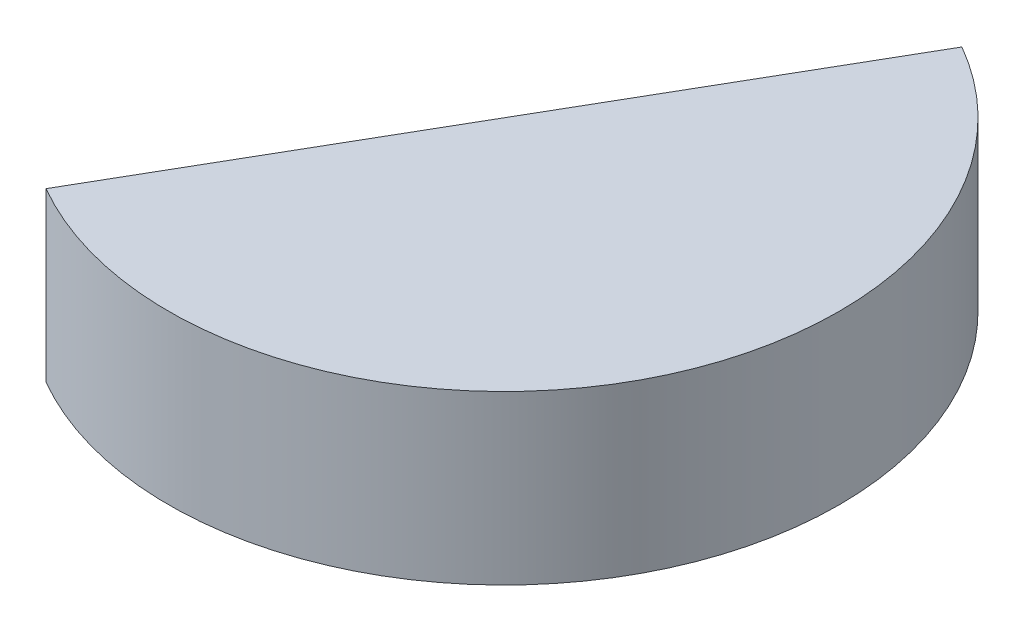
SolidWorks part; units mm, degrees
ref_plane "Front Plane" through (0, 0, 0) normal (0, 0, 1) x (1, 0, 0)
ref_plane "Top Plane" through (0, 0, 0) normal (0, 1, 0) x (1, 0, 0)
ref_plane "Right Plane" through (0, 0, 0) normal (1, 0, 0) x (0, 0, -1)
sketch "Sketch5" plane through (0, 0, 0) normal (1, 0, 0) x (0, 0, -1)
  line L1 (0, 0) -> (10000, 0)
  line L2 (0, 0) -> (0, 5000)
  line L3 (0, 5000) -> (10000, 5000)
  line L4 (10000, 0) -> (10000, 5000)
  dimension "D1" = 5000
  dimension "D2" = 10000
revolve "Revolve1" add sketch "Sketch5" angle 330 about L2
sketch "Sketch6" plane through (0, 5000, 0) normal (0, 1, 0) x (1, 0, 0)
  line L0 (0, 0) -> (-6270.9251, -10861.561)
  line L1 (-6270.9251, -10861.561) -> (-18667.3965, 4058.5601)
  line L2 (-18667.3965, 4058.5601) -> (972.4538, 11788.5213)
  line L3 (972.4538, 11788.5213) -> (0, 0)
  line L4 (5000, 8660.254) -> (0, 0) construction
  point P7 (915.3271, 11096.0065)
extrude "Cut-Extrude1" cut sketch "Sketch6" against normal through all both and the other way through all
